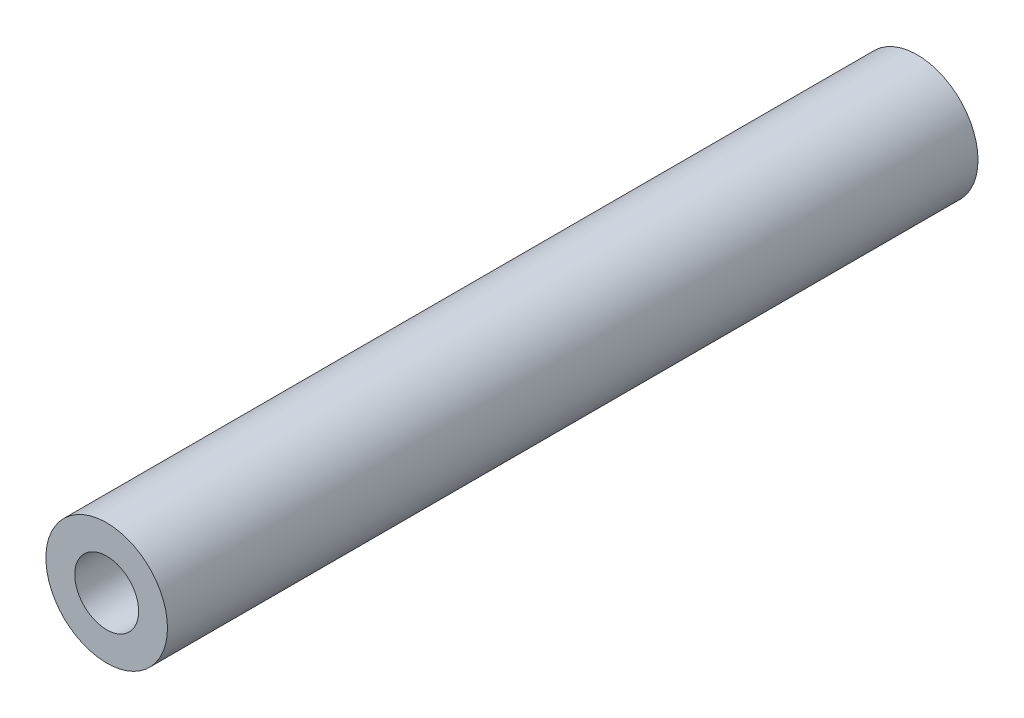
SolidWorks part; units mm, degrees
ref_plane "Plano frontal" through (0, 0, 0) normal (0, 0, 1) x (1, 0, 0)
ref_plane "Plano superior" through (0, 0, 0) normal (0, 1, 0) x (1, 0, 0)
ref_plane "Plano direito" through (0, 0, 0) normal (1, 0, 0) x (0, 0, -1)
sketch "Esboço1" plane through (0, 0, 0) normal (0, 0, 1) x (1, 0, 0)
  circle A0 centre (0, 0) radius 3
  dimension "D1" = 6
extrude "Ressalto-extrusão1" add sketch "Esboço1" along normal blind 40
hole_wizard "Broca de rosquear para helicoide M31" positions "Esboço3" profile "Esboço2" hole size "M3x0.5" standard "Ansi Metric"
sketch "Esboço3" plane through (0, 0, 0) normal (0, 0, -1) x (-1, 0, 0)
  point P0 (0, 0)
sketch "Esboço2" plane through (0, 0, 0) normal (1, 0, 0) x (0, 1, 0)
  line L0 (0, 0) -> (0, 4.9464)
  line L1 (0, 4.9464) -> (1.575, 4)
  line L2 (1.575, 4) -> (1.575, 0)
  line L5 (1.575, 0) -> (0, 0)
  line L10 (0, 4.9464) -> (-1.575, 4) construction
  line L11 (0, -6.35) -> (0, 107.95) construction
  dimension "Hole Dia." = 3.15
  dimension "Hole Depth" = 4
  dimension "Drill Angle" = 118
hole_wizard "Broca de rosquear para helicoide M32" positions "Esboço5" profile "Esboço4" hole size "M3x0.5" standard "Ansi Metric"
sketch "Esboço5" plane through (0, 0, 40) normal (0, 0, 1) x (1, 0, 0)
  point P0 (0, 0)
sketch "Esboço4" plane through (0, 0, 40) normal (1, 0, 0) x (0, -1, 0)
  line L0 (0, 0) -> (0, 4.9464)
  line L1 (0, 4.9464) -> (1.575, 4)
  line L2 (1.575, 4) -> (1.575, 0)
  line L5 (1.575, 0) -> (0, 0)
  line L10 (0, 4.9464) -> (-1.575, 4) construction
  line L11 (0, -6.35) -> (0, 107.95) construction
  dimension "Hole Dia." = 3.15
  dimension "Hole Depth" = 4
  dimension "Drill Angle" = 118
